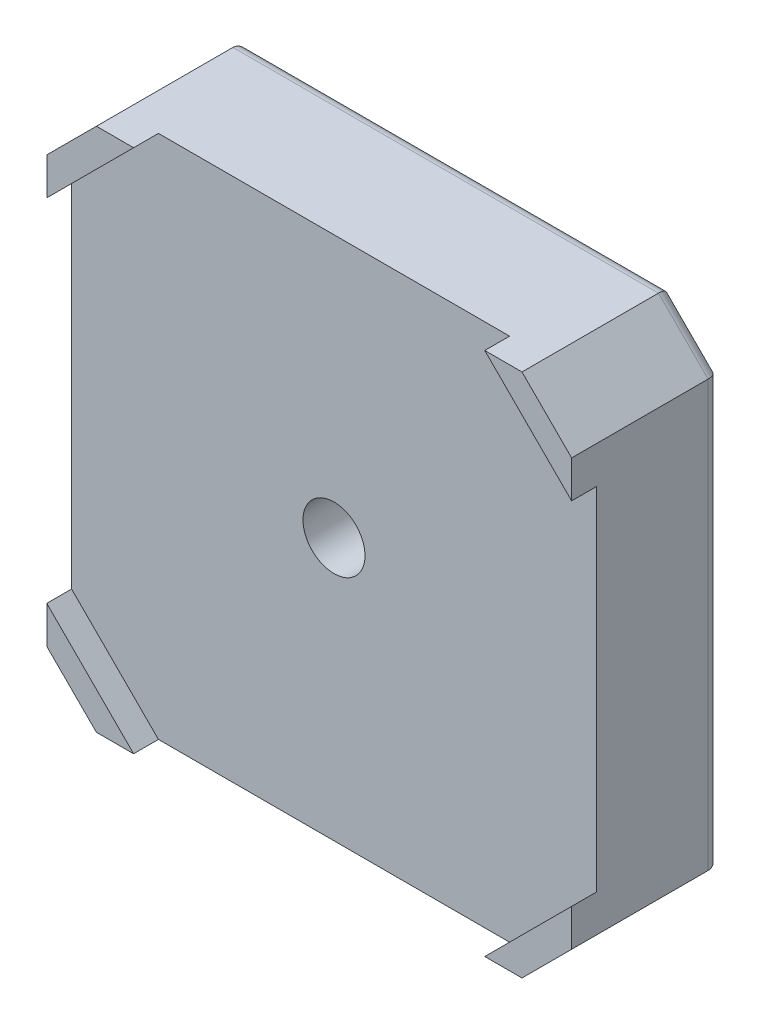
SolidWorks part; units mm, degrees
ref_plane "Front Plane" through (0, 0, 0) normal (0, 0, 1) x (1, 0, 0)
ref_plane "Top Plane" through (0, 0, 0) normal (0, 1, 0) x (1, 0, 0)
ref_plane "Right Plane" through (0, 0, 0) normal (1, 0, 0) x (0, 0, -1)
sketch "Sketch1" plane through (0, 0, 0) normal (0, 0, 1) x (1, 0, 0)
  line L0 (-42.3, 34.3) -> (-34.3, 42.3)
  line L1 (-34.3, -42.3) -> (34.3, -42.3)
  line L2 (-42.3, -34.3) -> (-42.3, 34.3)
  line L3 (-34.3, 42.3) -> (34.3, 42.3)
  line L4 (42.3, -34.3) -> (42.3, 34.3)
  line L5 (-42.3, -42.3) -> (42.3, 42.3) construction
  line L6 (-42.3, 42.3) -> (42.3, -42.3) construction
  line L7 (34.3, 42.3) -> (42.3, 34.3)
  line L8 (34.3, -42.3) -> (42.3, -34.3)
  line L9 (-42.3, -34.3) -> (-34.3, -42.3)
  point P0 (0, 0)
  dimension "D1" = 84.6
  dimension "D2" = 84.6
extrude "Boss-Extrude1" add sketch "Sketch1" along normal blind 24
sketch "Sketch2" plane through (0, 0, 24) normal (0, 0, 1) x (1, 0, 0)
  line L0 (-42.3, 28.3) -> (-28.3, 42.3)
  line L1 (-28.3, -42.3) -> (28.3, -42.3)
  line L2 (-42.3, -28.3) -> (-42.3, 28.3)
  line L3 (-28.3, 42.3) -> (28.3, 42.3)
  line L4 (42.3, -28.3) -> (42.3, 28.3)
  line L5 (-42.3, -42.3) -> (42.3, 42.3) construction
  line L6 (-42.3, 42.3) -> (42.3, -42.3) construction
  line L7 (28.3, 42.3) -> (42.3, 28.3)
  line L8 (28.3, -42.3) -> (42.3, -28.3)
  line L9 (-42.3, -28.3) -> (-28.3, -42.3)
  point P0 (0, 0)
  dimension "D1" = 84.6
  dimension "D2" = 84.6
extrude "Cut-Extrude1" cut sketch "Sketch2" against normal blind 4
sketch "Sketch3" plane through (0, 0, 0) normal (0, 0, -1) x (-1, 0, 0)
  circle A0 centre (0, 0) radius 22
  dimension "D1" = 44
extrude "Boss-Extrude2" add sketch "Sketch3" along normal blind 4
sketch "Sketch4" plane through (0, 0, -4) normal (0, 0, -1) x (-1, 0, 0)
  circle A0 centre (0, 0) radius 11
  dimension "D1" = 22
extrude "Cut-Extrude3" cut sketch "Sketch4" against normal blind 14
sketch "Sketch5" plane through (0, 0, 10) normal (0, 0, -1) x (-1, 0, 0)
  circle A0 centre (0, 0) radius 5
  dimension "D1" = 10
extrude "Cut-Extrude4" cut sketch "Sketch5" against normal through all
fillet "Fillet1" radius 2 8 edges at (-38.3, 38.3, 0) (-42.3, 0, 0) (-38.3, -38.3, 0) (0, -42.3, 0) (38.3, -38.3, 0) (42.3, 0, 0) (38.3, 38.3, 0) (0, 42.3, 0)
fillet "Fillet2" radius 1 3 edges at (-11, 0, -4) (-11, 0, 10) (-22, 0, -4)
sketch "Sketch6" plane through (0, 0, 0) normal (0, 0, -1) x (-1, 0, 0)
  line L1 (-31, -31) -> (31, -31) construction
  line L2 (-31, -31) -> (-31, 31) construction
  line L3 (-31, 31) -> (31, 31) construction
  line L4 (31, -31) -> (31, 31) construction
  line L5 (-31, -31) -> (31, 31) construction
  line L6 (-31, 31) -> (31, -31) construction
  circle A0 centre (-31, 31) radius 3
  circle A1 centre (31, 31) radius 3
  circle A2 centre (31, -31) radius 3
  circle A3 centre (-31, -31) radius 3
  point P0 (0, 0)
  dimension "D3" = 6
  dimension "D1" = 62
  dimension "D2" = 62
extrude "Cut-Extrude5" cut sketch "Sketch6" against normal blind 6
fillet "Fillet3" radius 1 4 edges at (28, -31, 0) (-34, -31, 0) (-34, 31, 0) (28, 31, 0)
